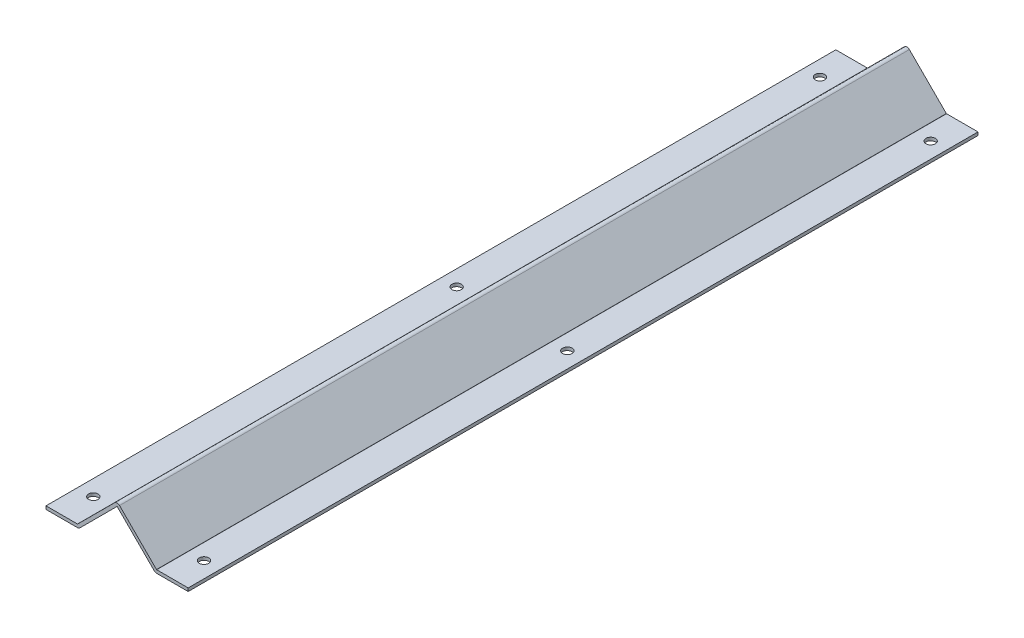
SolidWorks part; units mm, degrees
material "普通碳钢"
ref_plane "Front" through (0, 0, 0) normal (0, 0, 1) x (1, 0, 0)
ref_plane "Top" through (0, 0, 0) normal (0, 1, 0) x (1, 0, 0)
ref_plane "Right" through (0, 0, 0) normal (1, 0, 0) x (0, 0, -1)
sketch "草图1" plane through (0, 0, 0) normal (0, 0, 1) x (1, 0, 0)
  line L0 (0, 0) -> (19.9172, 0)
  line L1 (20.0586, 0.0586) -> (43.4444, 23.4444)
  line L2 (46.5556, 23.4444) -> (69.9414, 0.0586)
  line L3 (70.0828, 0) -> (90, 0)
  line L4 (0, -2) -> (19.9172, -2)
  line L5 (21.4728, -1.3556) -> (44.8586, 22.0302)
  line L6 (45.1414, 22.0302) -> (68.5272, -1.3556)
  line L7 (70.0828, -2) -> (90, -2)
  line L8 (0, 0) -> (0, -2)
  line L9 (90, 0) -> (90, -2)
  arc A0 (46.5556, 23.4444) -> (43.4444, 23.4444) centre (45, 21.8887) ccw
  arc A1 (20.0586, 0.0586) -> (19.9172, 0) centre (19.9172, 0.2) cw
  arc A2 (69.9414, 0.0586) -> (70.0828, 0) centre (70.0828, 0.2) ccw
  arc A3 (21.4728, -1.3556) -> (19.9172, -2) centre (19.9172, 0.2) cw
  arc A4 (45.1414, 22.0302) -> (44.8586, 22.0302) centre (45, 21.8887) ccw
  arc A5 (68.5272, -1.3556) -> (70.0828, -2) centre (70.0828, 0.2) ccw
  point P10 (45, 25)
  point P13 (20, 0)
  point P16 (70, 0)
  dimension "D6" = 2.2
  dimension "D7" = 0.2
  dimension "D8" = 0.2
  dimension "D1" = 135
  dimension "D2" = 135
  dimension "D3" = 25
  dimension "D4" = 20
  dimension "D5" = 20
  dimension "D9" = 2
extrude "凸台-拉伸1" add sketch "草图1" along normal blind 500
sketch "草图2" plane through (0, 0, 0) normal (0, 1, 0) x (1, 0, 0)
  line L0 (9.9586, 0) -> (9.9586, -500) construction
  line L1 (19.9172, 0) -> (0, 0) construction
  line L2 (19.9172, -500) -> (0, -500) construction
  line L3 (80.0414, 0) -> (80.0414, -500) construction
  line L4 (90, 0) -> (70.0828, 0) construction
  line L5 (90, -500) -> (70.0828, -500) construction
  line L6 (0, -250) -> (90, -250) construction
  line L7 (0, -500) -> (0, 0) construction
  line L8 (90, -500) -> (90, 0) construction
  line L9 (0, -20) -> (90, -20) construction
  line L10 (0, -480) -> (90, -480) construction
  circle A0 centre (9.9586, -20) radius 3
  circle A1 centre (80.0414, -20) radius 3
  circle A2 centre (9.9586, -250) radius 3
  circle A3 centre (80.0414, -250) radius 3
  circle A4 centre (9.9586, -480) radius 3
  circle A5 centre (80.0414, -480) radius 3
  dimension "D3" = 6
  dimension "D1" = 230
  dimension "D2" = 230
extrude "切除-拉伸1" cut sketch "草图2" against normal up to next
